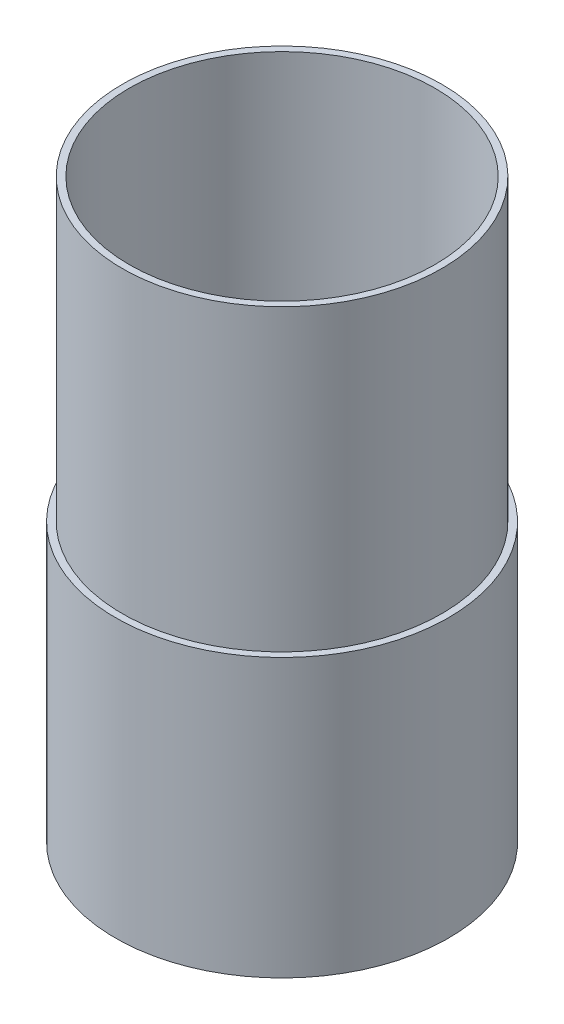
SolidWorks part; units mm, degrees
ref_plane "Front Plane" through (0, 0, 0) normal (0, 0, 1) x (1, 0, 0)
ref_plane "Top Plane" through (0, 0, 0) normal (0, 1, 0) x (1, 0, 0)
ref_plane "Right Plane" through (0, 0, 0) normal (1, 0, 0) x (0, 0, -1)
sketch "Sketch2" plane through (0, 0, 0) normal (0, 0, 1) x (1, 0, 0)
  line L1 (-4.064, 0) -> (-4.064, 82.55)
  line L2 (-4.064, 82.55) -> (-2.032, 82.55)
  line L3 (-2.032, 82.55) -> (-2.032, 171.45)
  line L4 (-2.032, 171.45) -> (0, 171.45)
  line L5 (0, 171.45) -> (0, 0)
  line L6 (0, 0) -> (45.466, 0) construction
  line L7 (45.466, 0) -> (45.466, 101.6) construction
  line L14 (0, 0) -> (-4.064, 0)
  dimension "D1" = 171.45
  dimension "D2" = 2.032
  dimension "D3" = 2.032
  dimension "D4" = 88.9
  dimension "D6" = 49.53
revolve "Revolve1" add sketch "Sketch2" angle 360 about L7
